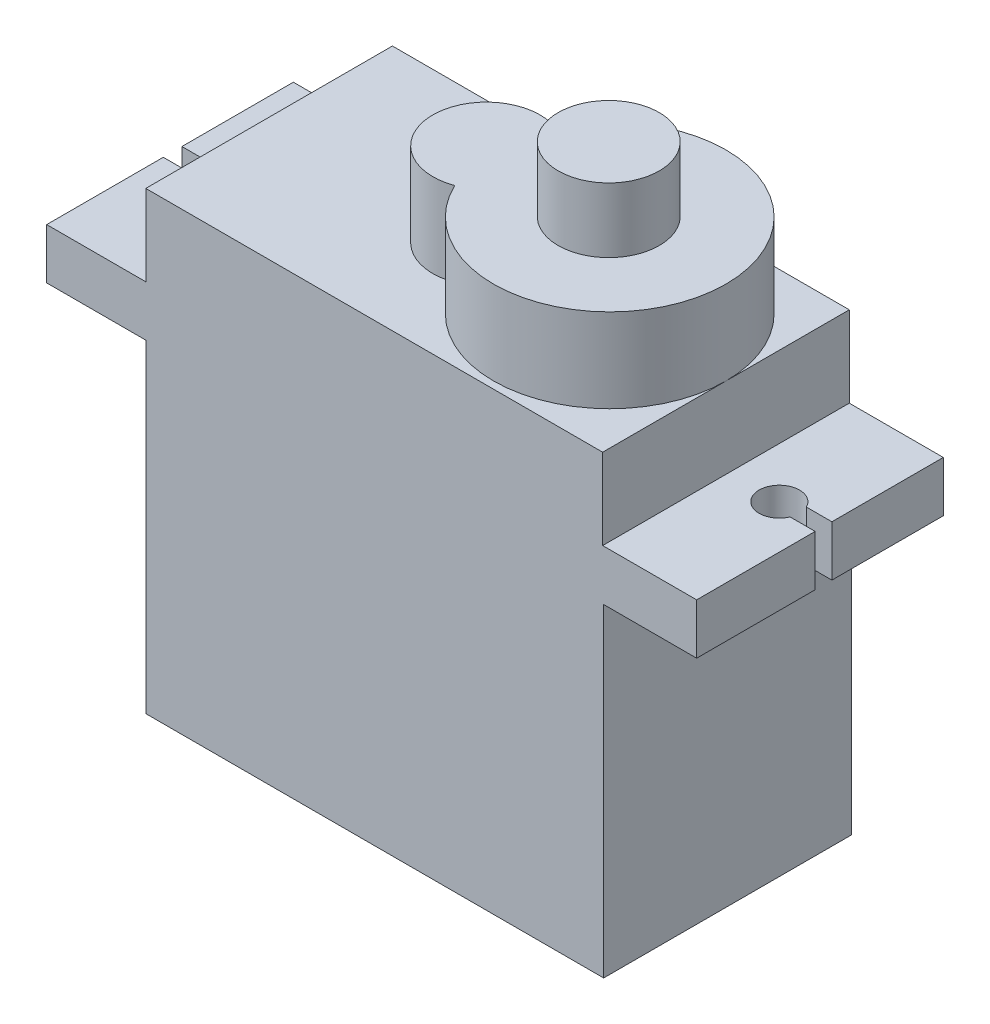
SolidWorks part; units mm, degrees
ref_plane "Front Plane" through (0, 0, 0) normal (0, 0, 1) x (1, 0, 0)
ref_plane "Top Plane" through (0, 0, 0) normal (0, 1, 0) x (1, 0, 0)
ref_plane "Right Plane" through (0, 0, 0) normal (1, 0, 0) x (0, 0, -1)
sketch "Sketch1" plane through (0, 0, 0) normal (0, 1, 0) x (1, 0, 0)
  line L1 (0, 0) -> (22.65, 0)
  line L2 (0, 0) -> (0, 12.25)
  line L3 (0, 12.25) -> (22.65, 12.25)
  line L4 (22.65, 0) -> (22.65, 12.25)
  dimension "D1" = 12.25
  dimension "D2" = 22.65
extrude "Boss-Extrude1" add sketch "Sketch1" along normal blind 16
sketch "Sketch2" plane through (0, 16, 0) normal (0, 1, 0) x (1, 0, 0)
  line L0 (0, 12.25) -> (0, 0) construction
  line L1 (-4.9, 12.2) -> (27.25, 12.2)
  line L2 (-4.9, 12.2) -> (-4.9, 0)
  line L3 (-4.9, 0) -> (27.25, 0)
  line L4 (27.25, 12.2) -> (27.25, 0)
  dimension "D1" = 32.15
  dimension "D2" = 4.9
extrude "Boss-Extrude2" add sketch "Sketch2" along normal blind 2.5
sketch "Sketch3" plane through (0, 18.5, 0) normal (0, 1, 0) x (1, 0, 0)
  line L0 (27.25, 12.2) -> (-4.9, 12.2) construction
  line L1 (0, 0) -> (22.6, 0)
  line L2 (0, 0) -> (0, 12.2)
  line L3 (0, 12.2) -> (22.6, 12.2)
  line L4 (22.6, 0) -> (22.6, 12.2)
  dimension "D1" = 22.6
extrude "Boss-Extrude3" add sketch "Sketch3" along normal blind 4
sketch "Sketch4" plane through (0, 22.5, 0) normal (0, 1, 0) x (1, 0, 0)
  line L0 (0, 6.1) -> (31.4466, 6.1) construction
  line L1 (0, 12.2) -> (0, 0) construction
  line L3 (22.6, 6.1) -> (22.6, 15.078) construction
  line L4 (22.6, 0) -> (22.6, 12.2) construction
  arc A2 (11.6656, 3.6132) -> (11.6656, 8.5868) centre (16.85, 6.1) ccw
  arc A3 (11.6656, 8.5868) -> (11.6656, 3.6132) centre (10.75, 6.1) ccw
  dimension "D1" = 5.75
  dimension "D2" = 5.3
  dimension "D3" = 11.85
extrude "Boss-Extrude4" add sketch "Sketch4" along normal blind 4.15
sketch "Sketch5" plane through (0, 26.65, 0) normal (0, 1, 0) x (1, 0, 0)
  line L0 (22.6, 0) -> (22.6, 6.1) construction
  circle A0 centre (16.8, 6.1) radius 2.5
  dimension "D1" = 5
  dimension "D2" = 5.8
extrude "Boss-Extrude5" add sketch "Sketch5" along normal blind 3.2
sketch "Sketch6" plane through (0, 18.5, 0) normal (0, 1, 0) x (1, 0, 0)
  line L0 (-4.9, 12.2) -> (-4.9, 0) construction
  line L1 (27.25, 0) -> (27.25, 12.2) construction
  line L3 (-3.6157, 5.7661) -> (-4.9, 5.7661)
  line L5 (-3.638, 6.6891) -> (-4.9, 6.6891)
  line L6 (-4.9, 5.7661) -> (-4.9, 6.6891)
  line L9 (26.012, 5.8619) -> (27.25, 5.8619)
  line L11 (25.988, 6.6891) -> (27.25, 6.6891)
  line L12 (27.25, 5.8619) -> (27.25, 6.6891)
  arc A0 (-3.6157, 5.7661) -> (-3.638, 6.6891) centre (-2.74, 6.249) ccw
  arc A1 (25.988, 6.6891) -> (26.012, 5.8619) centre (25.09, 6.249) ccw
  point P8 (-3.74, 6.249)
  point P13 (26.09, 6.249)
  dimension "D1" = 2
  dimension "D2" = 2
  dimension "D3" = 2.16
  dimension "D4" = 2.16
extrude "Cut-Extrude1" cut sketch "Sketch6" against normal through all
